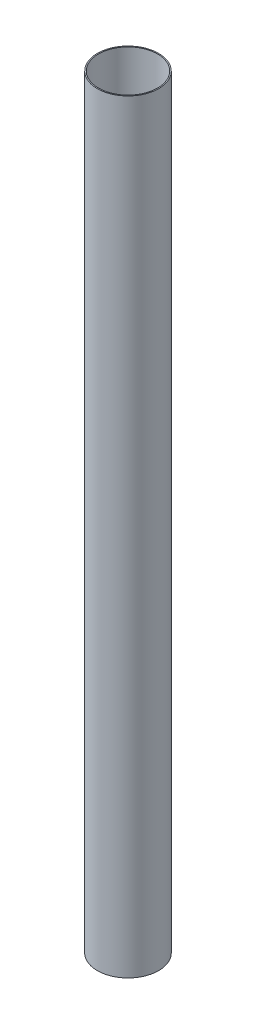
SolidWorks part; units mm, degrees
ref_plane "Front Plane" through (0, 0, 0) normal (0, 0, 1) x (1, 0, 0)
ref_plane "Top Plane" through (0, 0, 0) normal (0, 1, 0) x (1, 0, 0)
ref_plane "Right Plane" through (0, 0, 0) normal (1, 0, 0) x (0, 0, -1)
sketch "Sketch1" plane through (0, 0, 0) normal (0, 1, 0) x (1, 0, 0)
  circle A0 centre (0, 0) radius 42.5
  circle A1 centre (0, 0) radius 41
  dimension "D1" = 1.5
  dimension "D2" = 82
extrude "Boss-Extrude1" add sketch "Sketch1" along normal blind 1060
